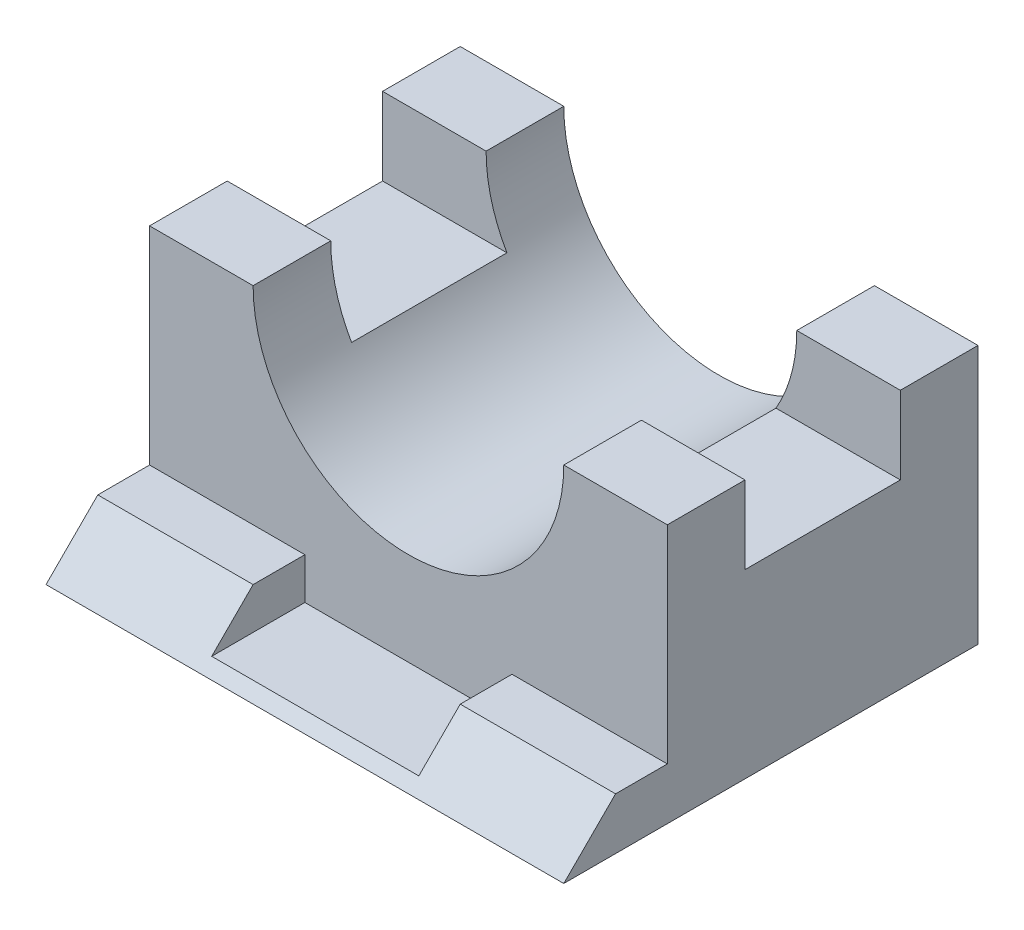
SolidWorks part; units mm, degrees
ref_plane "Front Plane" through (0, 0, 0) normal (0, 0, 1) x (1, 0, 0)
ref_plane "Top Plane" through (0, 0, 0) normal (0, 1, 0) x (1, 0, 0)
ref_plane "Right Plane" through (0, 0, 0) normal (1, 0, 0) x (0, 0, -1)
sketch "Sketch1" plane through (0, 0, 0) normal (1, 0, 0) x (0, 0, -1)
  line L0 (-40, 0) -> (40, 0)
  line L1 (40, 0) -> (40, 50)
  line L2 (40, 50) -> (25, 50)
  line L3 (25, 50) -> (25, 35)
  line L4 (25, 35) -> (-5, 35)
  line L5 (-5, 35) -> (-5, 50)
  line L6 (-5, 50) -> (-20, 50)
  line L7 (-20, 50) -> (-20, 10)
  line L8 (-20, 10) -> (-30, 10)
  line L9 (-30, 10) -> (-40, 0)
  point P4 (0, 0)
  dimension "D1" = 80
  dimension "D2" = 50
  dimension "D3" = 15
  dimension "D4" = 15
  dimension "D5" = 30
  dimension "D6" = 15
  dimension "D7" = 15
  dimension "D8" = 40
  dimension "D9" = 10
extrude "Boss-Extrude1" add sketch "Sketch1" along normal mid plane 100
sketch "Sketch2" plane through (0, 0, 20) normal (0, 0, 1) x (1, 0, 0)
  line L0 (0, 65.0971) -> (0, -16.7867) construction
  line L1 (50, 50) -> (-50, 50) construction
  line L2 (30, 50) -> (0, 50)
  line L3 (-30, 50) -> (30, 50)
  arc A0 (-30, 50) -> (30, 50) centre (0, 50) ccw
  line M4 (50, 50) -> (-50, 50)
  dimension "D1" = 60
extrude "Cut-Extrude1" cut sketch "Sketch2" against normal blind 100 contours L0 A0 M4 | L0 A0 M4
sketch "Sketch3" plane through (0, 0, 20) normal (0, 0, 1) x (1, 0, 0)
  line L0 (0, 63.0127) -> (0, -20.5761) construction
  line L1 (50, 10) -> (-50, 10) construction
  line L2 (-20, 10) -> (20, 10)
  line L3 (-20, 10) -> (-20, 2)
  line L4 (-20, 2) -> (20, 2)
  line L5 (20, 10) -> (20, 2)
  line L6 (50, 0) -> (-50, 0) construction
  point P11 (20, 6)
  dimension "D1" = 2
  dimension "D2" = 40
  dimension "D3" = 20
extrude "Cut-Extrude2" cut sketch "Sketch3" along normal blind 100
